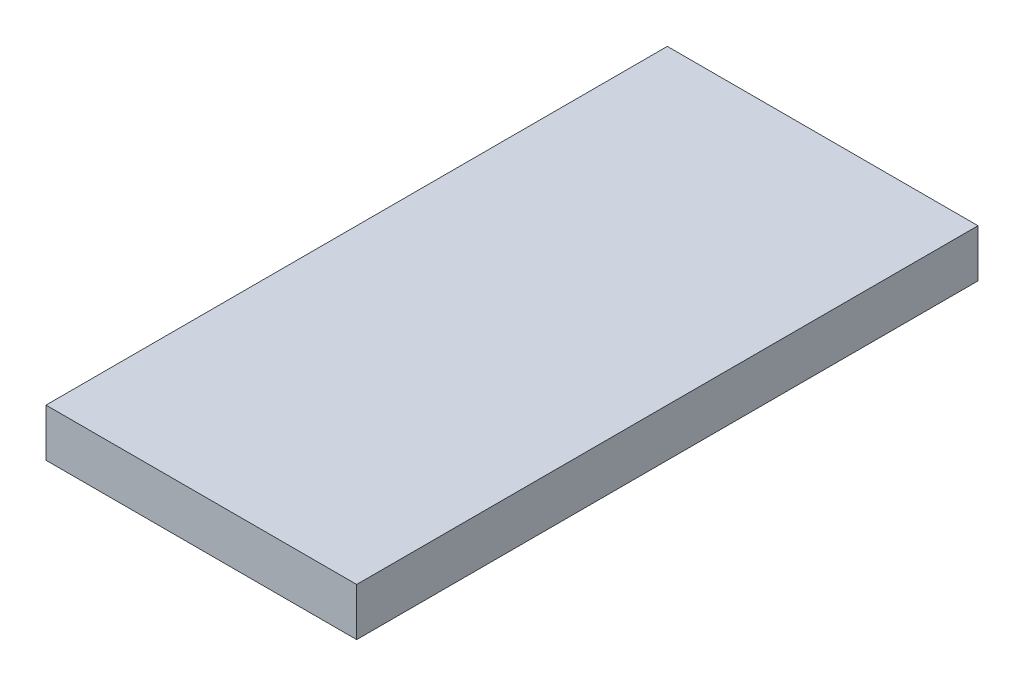
SolidWorks part; units mm, degrees
ref_plane "前视基准面" through (0, 0, 0) normal (0, 0, 1) x (1, 0, 0)
ref_plane "上视基准面" through (0, 0, 0) normal (0, 1, 0) x (1, 0, 0)
ref_plane "右视基准面" through (0, 0, 0) normal (1, 0, 0) x (0, 0, -1)
sketch "草图1" plane through (0, 0, 0) normal (0, 1, 0) x (1, 0, 0)
  line L1 (-32.5, -65) -> (32.5, -65)
  line L2 (-32.5, -65) -> (-32.5, 65)
  line L3 (-32.5, 65) -> (32.5, 65)
  line L4 (32.5, -65) -> (32.5, 65)
  line L5 (-32.5, -65) -> (32.5, 65) construction
  line L6 (-32.5, 65) -> (32.5, -65) construction
  point P0 (0, 0)
  dimension "D1" = 130
  dimension "D2" = 65
extrude "凸台-拉伸1" add sketch "草图1" along normal blind 10
